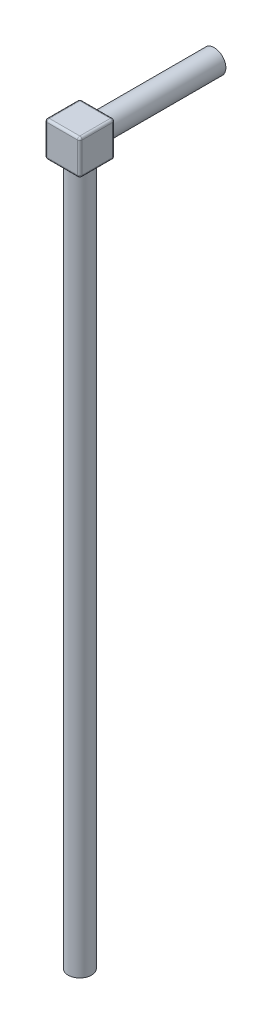
SolidWorks part; units mm, degrees
material "3.1645 (EN-AW 2030)"
ref_plane "前视基准面" through (0, 0, 0) normal (0, 0, 1) x (1, 0, 0)
ref_plane "上视基准面" through (0, 0, 0) normal (0, 1, 0) x (1, 0, 0)
ref_plane "右视基准面" through (0, 0, 0) normal (1, 0, 0) x (0, 0, -1)
sketch "Sketch1" plane through (0, 0, 0) normal (0, 1, 0) x (1, 0, 0)
  line L1 (-7.5, 7.5) -> (7.5, 7.5)
  line L2 (-7.5, 7.5) -> (-7.5, -7.5)
  line L3 (-7.5, -7.5) -> (7.5, -7.5)
  line L4 (7.5, 7.5) -> (7.5, -7.5)
  line L5 (-7.5, 7.5) -> (7.5, -7.5) construction
  line L6 (-7.5, -7.5) -> (7.5, 7.5) construction
  point P0 (0, 0)
  dimension "D1" = 15
  dimension "D2" = 15
extrude "Boss-Extrude1" add sketch "Sketch1" along normal mid plane 15
sketch "Sketch2" plane through (0, 0, -7.5) normal (0, 0, -1) x (-1, 0, 0)
  circle A0 centre (0, 0) radius 5
  dimension "D1" = 10
extrude "Boss-Extrude2" add sketch "Sketch2" along normal blind 50
sketch "Sketch3" plane through (0, -7.5, 0) normal (0, -1, 0) x (1, 0, 0)
  circle A0 centre (0, 0) radius 5
  dimension "D1" = 10
extrude "Boss-Extrude3" add sketch "Sketch3" along normal blind 300
fillet "Fillet1" radius 1 13 edges at (0, -7.5, -7.5) (0, -7.5, 7.5) (0, -7.5, 5) (-7.5, 0, -7.5) (-7.5, 0, 7.5) (-7.5, -7.5, 0) (0, 7.5, 7.5) (-7.5, 7.5, 0) (0, 7.5, -7.5) (7.5, 0, 7.5) (7.5, 7.5, 0) (7.5, 0, -7.5) (7.5, -7.5, 0)
